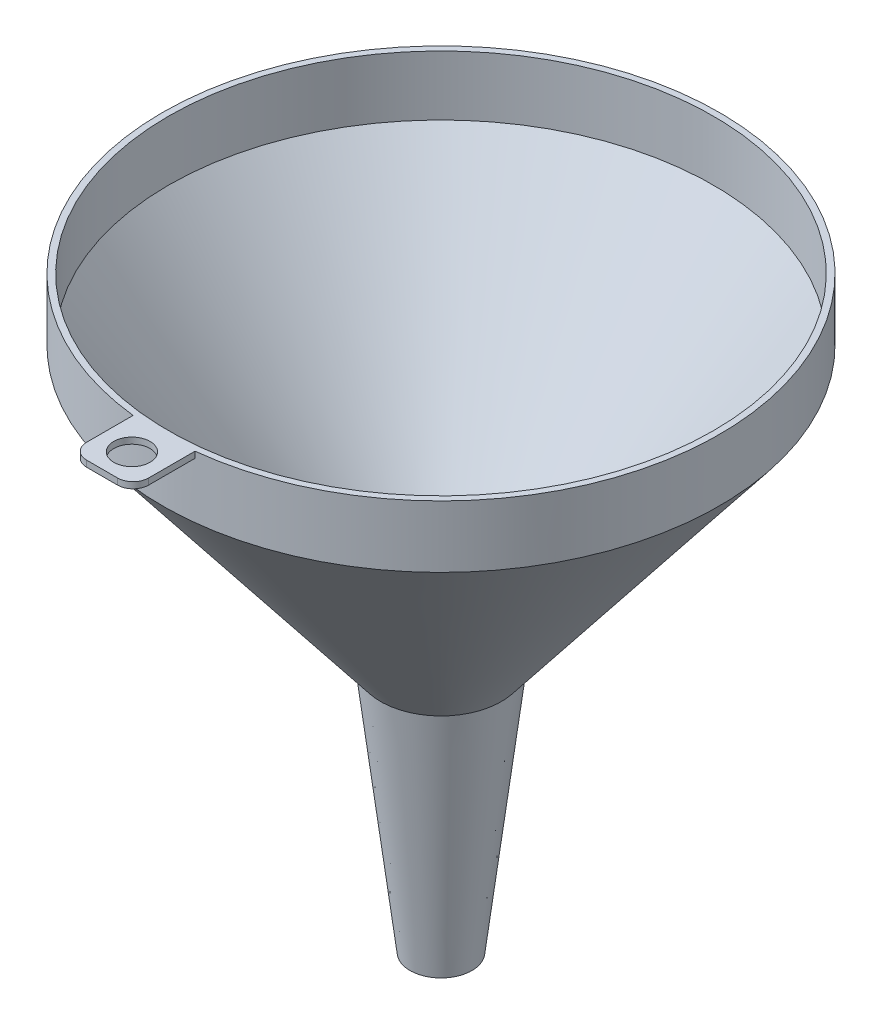
SolidWorks part; units mm, degrees
ref_plane "Alzado" through (0, 0, 0) normal (0, 0, 1) x (1, 0, 0)
ref_plane "Planta" through (0, 0, 0) normal (0, 1, 0) x (1, 0, 0)
ref_plane "Vista lateral" through (0, 0, 0) normal (1, 0, 0) x (0, 0, -1)
sketch "Croquis1" plane through (0, 0, 0) normal (0, 0, 1) x (1, 0, 0)
  line L0 (0, 95) -> (0, -95)
  line L1 (0, -95) -> (10, -95)
  line L2 (10, -95) -> (19.5094, -15)
  line L3 (19.5094, -15) -> (90, 75)
  line L4 (90, 75) -> (90, 95)
  line L5 (90, 95) -> (0, 95)
  dimension "D1" = 190
  dimension "D2" = 10
  dimension "D3" = 80
  dimension "D4" = 20
  dimension "D5" = 90
  dimension "D6" = 19.5094
revolve "Revolución1" add sketch "Croquis1" angle 360 about L0
shell "Vaciado1" thickness 2
ref_plane "Plano1" through (0, 95, 0) normal (0, 1, 0) x (1, 0, 0)
sketch "Croquis2" plane through (0, 95, 0) normal (0, 1, 0) x (1, 0, 0)
  line L0 (0, -90) -> (0, -109.4427)
  line L3 (10, -89.4427) -> (10, -109.4427)
  line L4 (10, -109.4427) -> (-10, -109.4427)
  line L5 (-10, -89.4427) -> (-10, -109.4427)
  line L6 (3.8743, -116.622) -> (-10, -109.4427) construction
  line L7 (10, -109.4427) -> (-36.1202, -133.3078) construction
  circle A0 centre (0, 0) radius 90 construction
  arc A1 (-10, -89.4427) -> (10, -89.4427) centre (0, 0) ccw
  point P6 (0, -114.6173)
  dimension "D1" = 20
  dimension "D2" = 20
extrude "Saliente-Extruir1" add sketch "Croquis2" against normal blind 2 contours A1 L5 L4 L0 | A1 L0 L4 L3
sketch "Croquis3" plane through (0, 95, 0) normal (0, 1, 0) x (1, 0, 0)
  circle A0 centre (0, -99.8178) radius 5.8556
extrude "Cortar-Extruir1" cut sketch "Croquis3" against normal blind 22
fillet "Redondeo1" radius 5 2 edges at (10, 94, 109.4427) (-10, 94, 109.4427)
